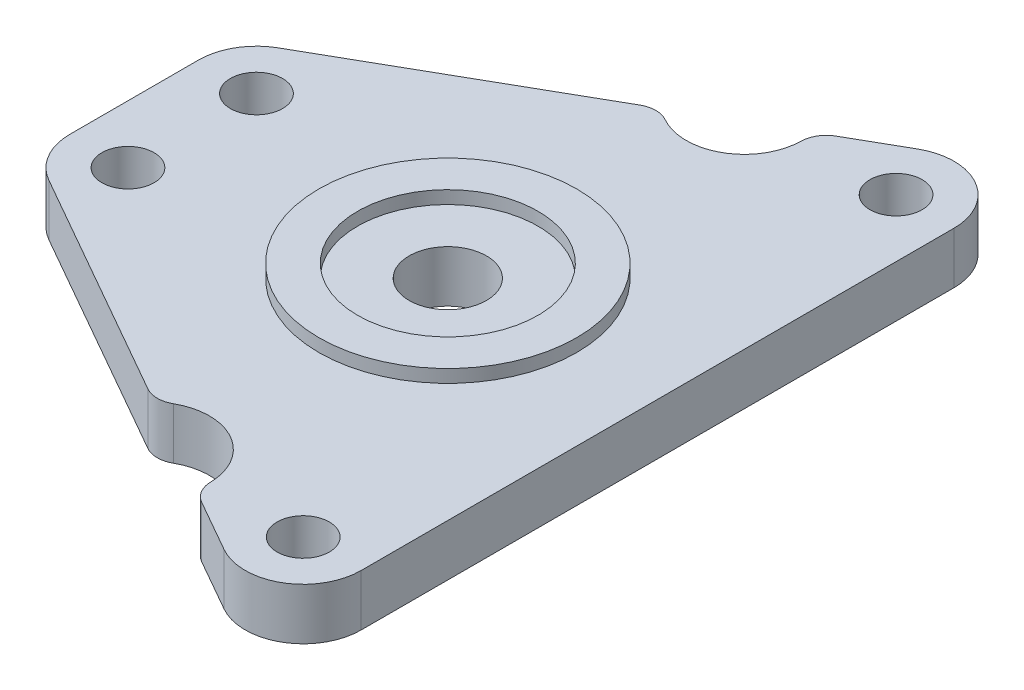
SolidWorks part; units mm, degrees
ref_plane "Front Plane" through (0, 0, 0) normal (0, 0, 1) x (1, 0, 0)
ref_plane "Top Plane" through (0, 0, 0) normal (0, 1, 0) x (1, 0, 0)
ref_plane "Right Plane" through (0, 0, 0) normal (1, 0, 0) x (0, 0, -1)
sketch "Sketch1" plane through (0, 0, 0) normal (0, 1, 0) x (1, 0, 0)
  line L0 (0, 4.985) -> (4.5, 4.985) construction
  line L1 (0, -4.985) -> (4.5, -4.985) construction
  line L2 (40.61, -23) -> (36.11, -23) construction
  line L3 (40.61, 23) -> (36.11, 23) construction
  line L4 (2.2718, -8.8946) -> (21.2557, -19.7138)
  line L5 (0, -4.985) -> (0, 4.985)
  line L6 (2.2718, 8.8946) -> (21.2557, 19.7138)
  line L7 (40.61, 23) -> (40.61, -23)
  line L8 (36.11, 23) -> (24.33, 23) construction
  line L9 (36.11, -23) -> (24.33, -23) construction
  line L10 (28.7242, -23.9702) -> (33.8818, -26.9096)
  line L11 (28.7242, 23.9702) -> (33.8818, 26.9096)
  line L12 (24.33, -23) -> (24.33, 23) construction
  arc A0 (2.2718, 8.8946) -> (0, 4.985) centre (4.5, 4.985) ccw
  arc A1 (0, -4.985) -> (2.2718, -8.8946) centre (4.5, -4.985) ccw
  arc A2 (40.61, 23) -> (33.8818, 26.9096) centre (36.11, 23) ccw
  arc A3 (33.8818, -26.9096) -> (40.61, -23) centre (36.11, -23) ccw
  arc A4 (21.2557, 19.7138) -> (28.7242, 23.9702) centre (24.33, 23) ccw
  arc A5 (28.7242, -23.9702) -> (21.2557, -19.7138) centre (24.33, -23) ccw
  circle A6 centre (36.11, -23) radius 2.025
  circle A7 centre (36.11, 23) radius 2.025
  circle A8 centre (4.5, 4.985) radius 2.025
  circle A9 centre (4.5, -4.985) radius 2.025
  circle A10 centre (24.33, 0) radius 3
  point P0 (0, 0)
  point P1 (40.61, 0)
  dimension "D5" = 4.05
  dimension "D6" = 6
  dimension "D3" = 46
  dimension "D1" = 4.5
  dimension "D2" = 9.97
  dimension "D4" = 11.78
  dimension "D7" = 40.61
extrude "Boss-Extrude1" add sketch "Sketch1" along normal blind 4
sketch "Sketch2" plane through (0, 4, 0) normal (0, 1, 0) x (1, 0, 0)
  circle A1 centre (24.33, 0) radius 7
  circle A3 centre (24.33, 0) radius 10
  circle A4 centre (24.33, 0) radius 3 construction
  dimension "D1" = 14
  dimension "D2" = 20
extrude "Boss-Extrude2" add sketch "Sketch2" along normal blind 1
fillet "Fillet1" radius 2 4 edges at (28.7242, 2, -23.9702) (21.2557, 2, -19.7138) (28.7242, 2, 23.9702) (21.2557, 2, 19.7138)
